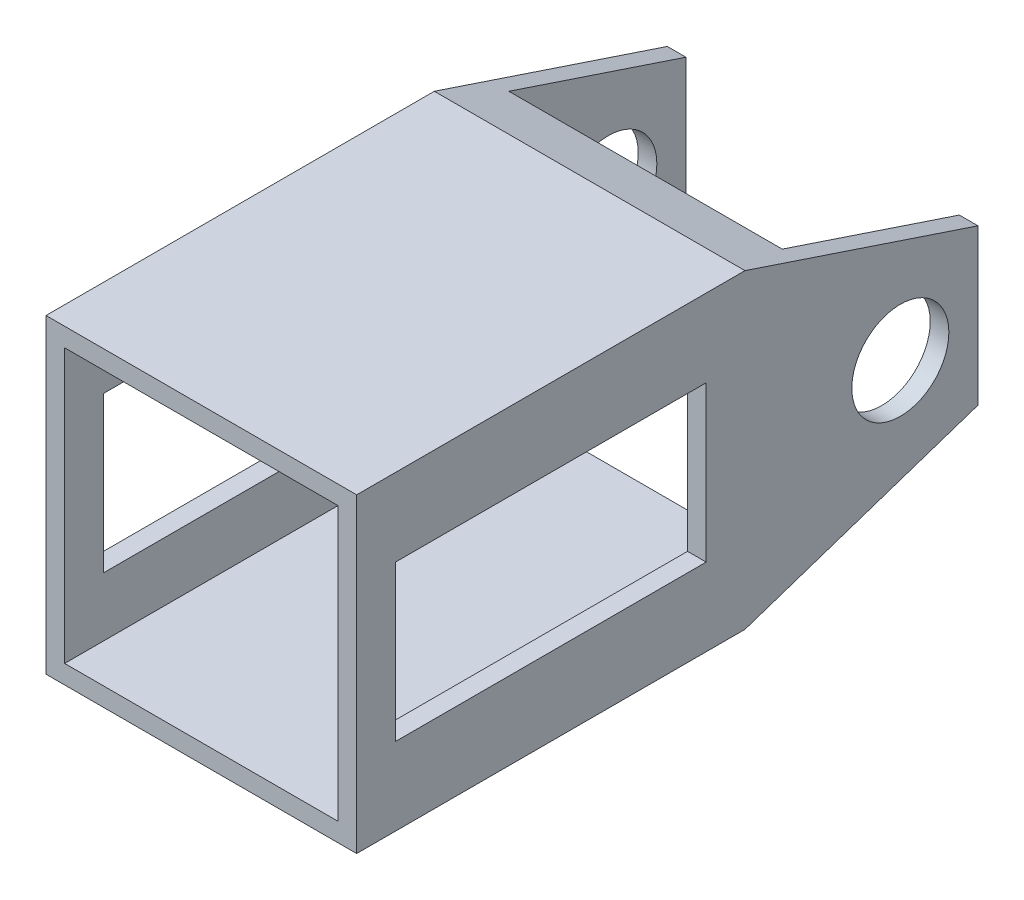
SolidWorks part; units mm, degrees
ref_plane "Front Plane" through (0, 0, 0) normal (0, 0, 1) x (1, 0, 0)
ref_plane "Top Plane" through (0, 0, 0) normal (0, 1, 0) x (1, 0, 0)
ref_plane "Right Plane" through (0, 0, 0) normal (1, 0, 0) x (0, 0, -1)
sketch "Sketch1" plane through (0, 0, 0) normal (0, 0, 1) x (1, 0, 0)
  line L1 (-12.7, -12.7) -> (12.7, -12.7)
  line L2 (-12.7, -12.7) -> (-12.7, 12.7)
  line L3 (-12.7, 12.7) -> (12.7, 12.7)
  line L4 (12.7, -12.7) -> (12.7, 12.7)
  line L5 (-12.7, -12.7) -> (12.7, 12.7) construction
  line L6 (-12.7, 12.7) -> (12.7, -12.7) construction
  line L7 (-11.176, -11.176) -> (11.176, -11.176)
  line L8 (-11.176, -11.176) -> (-11.176, 11.176)
  line L9 (-11.176, 11.176) -> (11.176, 11.176)
  line L10 (11.176, -11.176) -> (11.176, 11.176)
  line L11 (-11.176, -11.176) -> (11.176, 11.176) construction
  line L12 (-11.176, 11.176) -> (11.176, -11.176) construction
  point P0 (0, 0)
  point P6 (0, 0)
  point P13 (6.6003, 14.224)
  point P14 (7.0311, -14.224)
  point P15 (-7.874, -11.3844)
  point P16 (7.874, -11.0254)
  dimension "D1" = 25.4
  dimension "D2" = 25.4
  dimension "D3" = 1.524
  dimension "D4" = 1.524
extrude "Boss-Extrude1" add sketch "Sketch1" along normal mid plane 50.8
sketch "Sketch2" plane through (12.7, 0, 0) normal (1, 0, 0) x (0, 0, -1)
  line L0 (-25.4, -12.7) -> (-25.4, 12.7) construction
  line L1 (-22.225, -6.35) -> (3.175, -6.35)
  line L2 (-22.225, -6.35) -> (-22.225, 6.35)
  line L3 (-22.225, 6.35) -> (3.175, 6.35)
  line L4 (3.175, -6.35) -> (3.175, 6.35)
  line L5 (-22.225, -6.35) -> (3.175, 6.35) construction
  line L6 (-22.225, 6.35) -> (3.175, -6.35) construction
  circle A0 centre (19.05, 0) radius 3.9688
  point P0 (-9.525, 0)
  point P10 (0, 0)
  dimension "D4" = 7.9375
  dimension "D1" = 25.4
  dimension "D2" = 12.7
  dimension "D3" = 3.175
  dimension "D5" = 15.875
extrude "Cut-Extrude1" cut sketch "Sketch2" against normal through all
sketch "Sketch3" plane through (12.7, 0, 0) normal (1, 0, 0) x (0, 0, -1)
  line L0 (6.35, 12.7) -> (25.4, 6.35)
  line L1 (-25.4, 12.7) -> (25.4, 12.7) construction
  line L2 (25.4, -12.7) -> (25.4, 12.7) construction
  line L3 (25.4, 6.35) -> (25.4, 12.7)
  line L4 (25.4, 12.7) -> (6.35, 12.7)
  line L5 (13.97, 0) -> (-13.97, 0) construction
  line L6 (25.4, -6.35) -> (25.4, -12.7)
  line L7 (6.35, -12.7) -> (25.4, -6.35)
  line L8 (25.4, -12.7) -> (6.35, -12.7)
  dimension "D1" = 19.05
  dimension "D2" = 6.35
extrude "Cut-Extrude2" cut sketch "Sketch3" against normal through all
